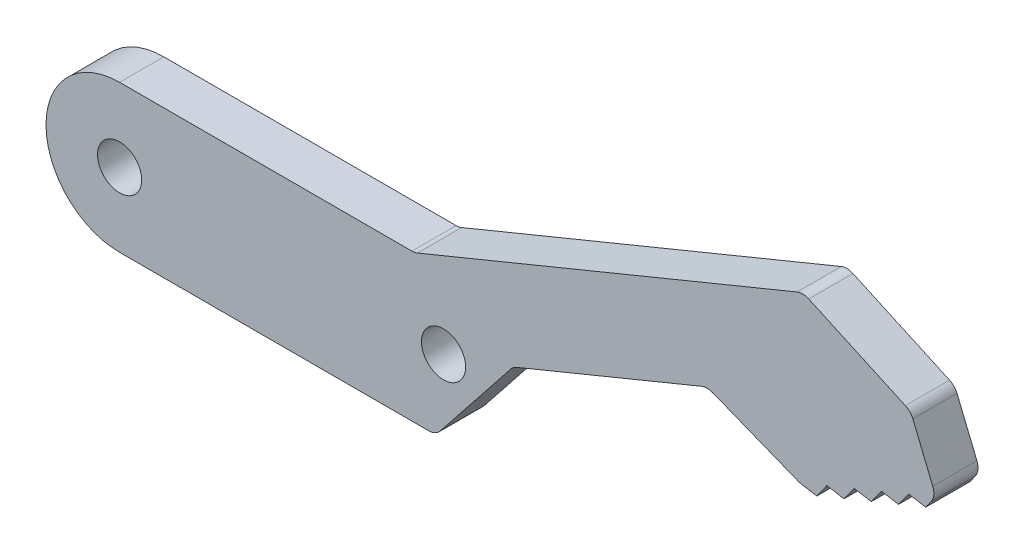
SolidWorks part; units mm, degrees
ref_plane "Front Plane" through (0, 0, 0) normal (0, 0, 1) x (1, 0, 0)
ref_plane "Top Plane" through (0, 0, 0) normal (0, 1, 0) x (1, 0, 0)
ref_plane "Right Plane" through (0, 0, 0) normal (1, 0, 0) x (0, 0, -1)
sketch "Sketch1" plane through (0, 0, 0) normal (0, 0, 1) x (1, 0, 0)
  line L0 (0, 0) -> (22, 0) construction
  line L1 (0, 5) -> (22, 5)
  line L2 (0, -5) -> (22, -5)
  line L3 (20.05, 5) -> (23.9914, -4.5863) construction
  line L4 (20.05, 5) -> (51.4959, 17.929) construction
  line L5 (23.9914, -4.5863) -> (55.4373, 8.3426) construction
  line L6 (51.4959, 17.929) -> (55.4373, 8.3426) construction
  line L7 (20.05, 5) -> (46.409, 15.8375)
  line L8 (46.409, 15.8375) -> (53.7261, 12.5046)
  line L9 (53.7261, 12.5046) -> (55.4373, 8.3426)
  line L10 (55.4373, 8.3426) -> (46.1885, 4.54)
  line L11 (46.1885, 4.54) -> (39.9002, 7.0361)
  line L12 (39.9002, 7.0361) -> (26.7299, 1.6211)
  line L13 (46.1885, 4.54) -> (47.351, 4.3422)
  line L14 (47.351, 4.3422) -> (48.0382, 5.3005)
  line L15 (47.351, 4.3422) -> (54.7501, 7.3843) construction
  line L16 (48.0382, 5.3005) -> (49.2008, 5.1027)
  line L17 (49.2008, 5.1027) -> (49.888, 6.0611)
  line L18 (49.888, 6.0611) -> (51.0505, 5.8633)
  line L19 (51.0505, 5.8633) -> (51.7378, 6.8216)
  line L20 (51.7378, 6.8216) -> (52.9003, 6.6238)
  line L21 (52.9003, 6.6238) -> (53.5875, 7.5821)
  line L22 (53.5875, 7.5821) -> (54.7501, 7.3843)
  line L23 (54.7501, 7.3843) -> (55.4373, 8.3426)
  line L24 (26.7299, 1.6211) -> (21.4748, -5)
  arc A0 (0, 5) -> (0, -5) centre (0, 0) ccw
  arc A1 (22, -5) -> (22, 5) centre (22, 0) ccw
  circle A2 centre (0, 0) radius 1.5
  circle A3 centre (22, 0) radius 1.5
  point P3 (11, 0)
  point P26 (21.4748, -5)
  dimension "D11" = 3
  dimension "D12" = 3
  dimension "D1" = 10
  dimension "D2" = 22
  dimension "D3" = 157.65
  dimension "D4" = 1.95
  dimension "D5" = 34
  dimension "D6" = 14.24
  dimension "D7" = 10
  dimension "D8" = 4.5
  dimension "D9" = 5.5
  dimension "D10" = 136
  dimension "D13" = 2
  dimension "D14" = 0.625
  dimension "D15" = 8
  dimension "D16" = 2
  dimension "D17" = 2
  dimension "D18" = 2
extrude "Boss-Extrude1" add sketch "Sketch1" along normal blind 3 contours A1 L1 A0 L2 A3 A2 | A1 L12 L11 L10 L9 L8 L7 L1 | L13 L14 L10 | L20 L21 L10 | L18 L19 L10 | L22 L23 L10 | L16 L17 L10
fillet "Fillet1" radius 1 8 edges at (46.1885, 4.54, 1.5) (55.4373, 8.3426, 1.5) (53.7261, 12.5046, 1.5) (46.409, 15.8375, 1.5) (20.05, 5, 1.5) (39.9002, 7.0361, 1.5) (21.4748, -5, 1.5) (26.7299, 1.6211, 1.5)
